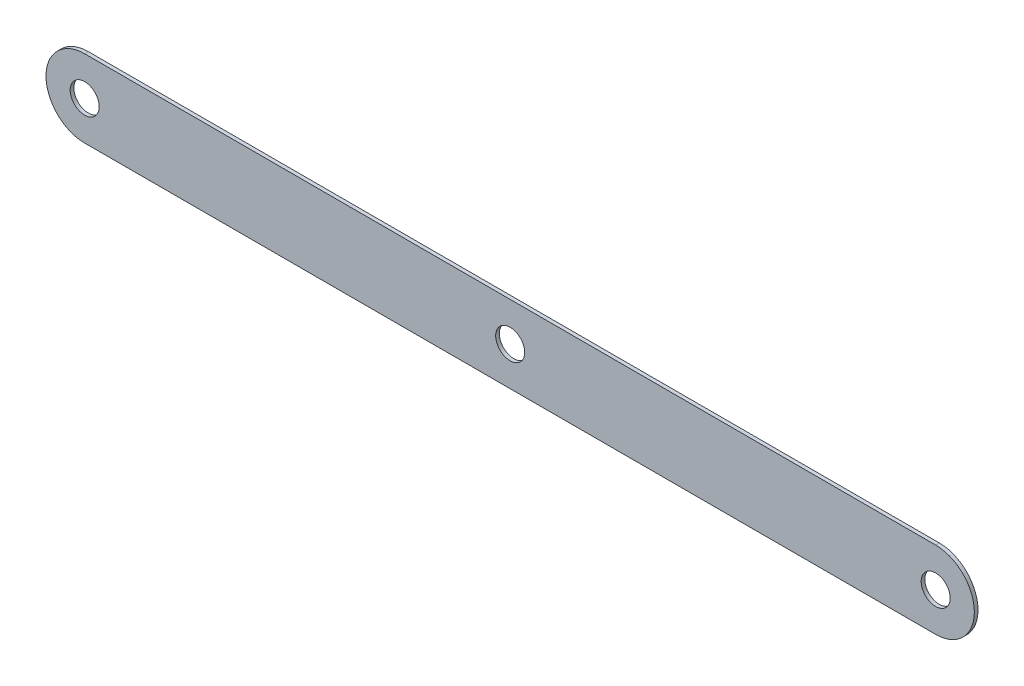
SolidWorks part; units mm, degrees
material "Alloy Steel"
ref_plane "Front" through (0, 0, 0) normal (0, 0, 1) x (1, 0, 0)
ref_plane "Top" through (0, 0, 0) normal (0, 1, 0) x (1, 0, 0)
ref_plane "Right" through (0, 0, 0) normal (1, 0, 0) x (0, 0, -1)
sketch "Sketch1" plane through (0, 0, 0) normal (0, 0, 1) x (1, 0, 0)
  line L1 (-139.7, 12.7) -> (139.7, 12.7)
  line L2 (-139.7, 12.7) -> (-139.7, -12.7)
  line L3 (-139.7, -12.7) -> (139.7, -12.7)
  line L4 (139.7, 12.7) -> (139.7, -12.7)
  line L5 (-139.7, 12.7) -> (139.7, -12.7) construction
  line L6 (-139.7, -12.7) -> (139.7, 12.7) construction
  arc A0 (-139.7, 12.7) -> (-139.7, -12.7) centre (-139.7, 0) ccw
  arc A1 (139.7, 12.7) -> (139.7, -12.7) centre (139.7, 0) cw
  point P0 (0, 0)
  dimension "D3" = 12.7
  dimension "D1" = 279.4
  dimension "D2" = 25.4
extrude "Boss-Extrude1" add sketch "Sketch1" along normal blind 1.2 contours L4 L1 L2 L3 | A1 L4 | L2 A0
sketch "Sketch2" plane through (0, 0, 1.2) normal (0, 0, 1) x (1, 0, 0)
  circle A0 centre (0, 0) radius 4.7625
  dimension "D1" = 9.525
extrude "Cut-Extrude1" cut sketch "Sketch2" against normal through all
sketch "Sketch3" plane through (0, 0, 1.2) normal (0, 0, 1) x (1, 0, 0)
  circle A0 centre (-139.7, 0) radius 4.7625
  circle A1 centre (139.7, 0) radius 4.7625
  dimension "D1" = 9.525
  dimension "D2" = 9.525
extrude "Cut-Extrude2" cut sketch "Sketch3" against normal through all
